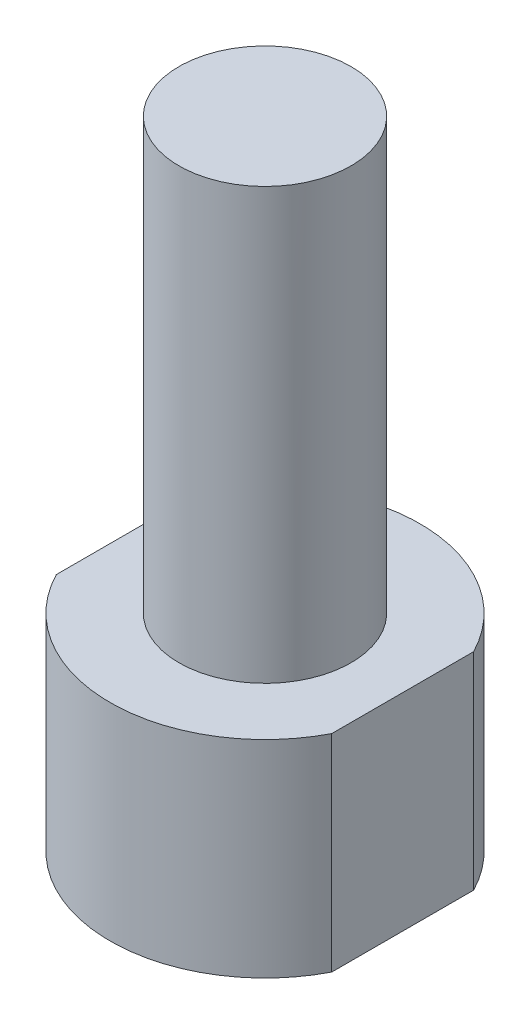
SolidWorks part; units mm, degrees
ref_plane "前视基准面" through (0, 0, 0) normal (0, 0, 1) x (1, 0, 0)
ref_plane "上视基准面" through (0, 0, 0) normal (0, 1, 0) x (1, 0, 0)
ref_plane "右视基准面" through (0, 0, 0) normal (1, 0, 0) x (0, 0, -1)
ref_plane "基准面4" through (0, 12, 0) normal (0, 1, 0) x (1, 0, 0)
sketch "草图1" plane through (0, 12, 0) normal (0, 1, 0) x (1, 0, 0)
  line L0 (-8, 4.1231) -> (-8, -4.1231)
  line L1 (8, -4.1231) -> (8, 4.1231)
  arc A0 (8, 4.1231) -> (-8, 4.1231) centre (0, 0) ccw
  arc A1 (-8, -4.1231) -> (8, -4.1231) centre (0, 0) ccw
extrude "凸台-拉伸1" add sketch "草图1" against normal blind 12
sketch "草图2" plane through (0, 0, 0) normal (0, 0, 1) x (1, 0, 0)
  line L0 (5, 37) -> (0, 37)
  line L1 (0, 37) -> (0, 12)
  line L2 (0, 12) -> (5, 12)
  line L3 (5, 12) -> (5, 37)
  line L4 (0, 37) -> (0, 12) construction
revolve "旋转1" add sketch "草图2" angle 360 about L4
